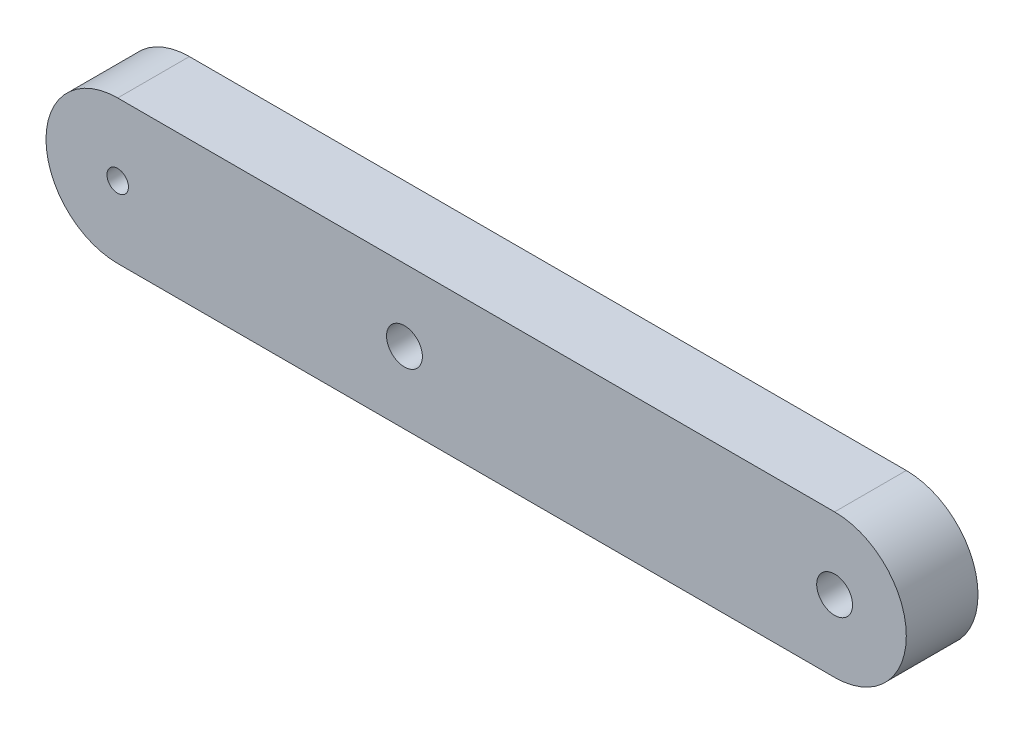
SolidWorks part; units mm, degrees
ref_plane "Plan de face" through (0, 0, 0) normal (0, 0, 1) x (1, 0, 0)
ref_plane "Plan de dessus" through (0, 0, 0) normal (0, 1, 0) x (1, 0, 0)
ref_plane "Plan de droite" through (0, 0, 0) normal (1, 0, 0) x (0, 0, -1)
sketch "Esquisse1" plane through (0, 0, 0) normal (0, 0, 1) x (1, 0, 0)
  line L1 (-40, 0) -> (60, 0)
  line L3 (-40, 20) -> (60, 20)
  arc A1 (60, 20) -> (60, 0) centre (60, 10) cw
  circle A2 centre (0, 10) radius 2.5
  circle A3 centre (60, 10) radius 2.5
  arc A9 (-40, 20) -> (-40, 0) centre (-40, 10) ccw
  circle A10 centre (-40, 9.9836) radius 1.5
  dimension "D1" = 5
  dimension "D2" = 5
  dimension "D5" = 100
  dimension "D6" = 3
  dimension "D7" = 40
  dimension "D3" = 20
  dimension "D4" = 100
  dimension "D10" = 60
extrude "Boss.-Extru.1" add sketch "Esquisse1" along normal blind 10
